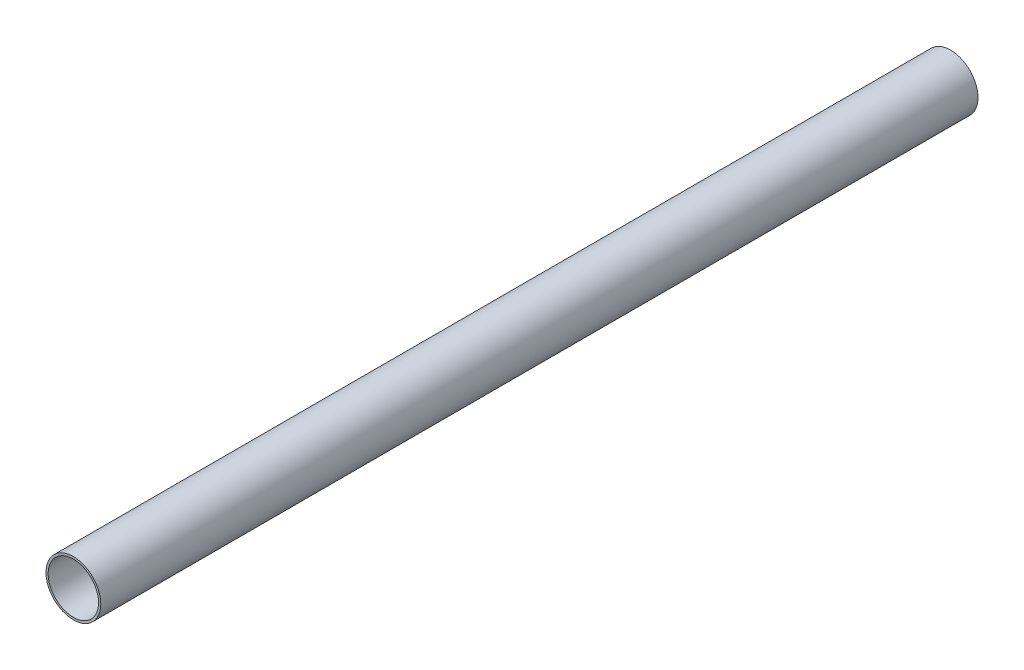
SolidWorks part; units mm, degrees
ref_plane "Front Plane" through (0, 0, 0) normal (0, 0, 1) x (1, 0, 0)
ref_plane "Top Plane" through (0, 0, 0) normal (0, 1, 0) x (1, 0, 0)
ref_plane "Right Plane" through (0, 0, 0) normal (1, 0, 0) x (0, 0, -1)
sketch "Sketch1" plane through (0, 0, 0) normal (0, 0, 1) x (1, 0, 0)
  circle A0 centre (0, 0) radius 12.5
  circle A1 centre (0, 0) radius 11.5
  dimension "D1" = 25
  dimension "D2" = 23
extrude "Boss-Extrude1" add sketch "Sketch1" along normal mid plane 400
